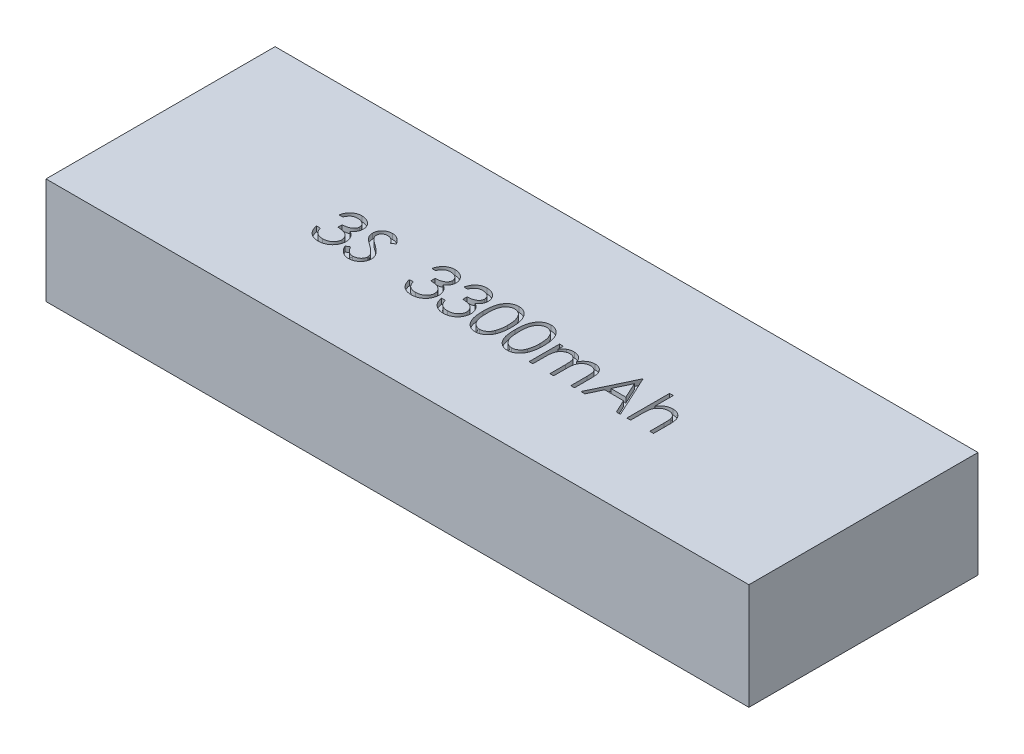
SolidWorks part; units mm, degrees
ref_plane "Front Plane" through (0, 0, 0) normal (0, 0, 1) x (1, 0, 0)
ref_plane "Top Plane" through (0, 0, 0) normal (0, 1, 0) x (1, 0, 0)
ref_plane "Right Plane" through (0, 0, 0) normal (1, 0, 0) x (0, 0, -1)
sketch "Sketch1" plane through (0, 0, 0) normal (0, 1, 0) x (1, 0, 0)
  line L1 (0, 0) -> (135, 0)
  line L2 (0, 0) -> (0, 44)
  line L3 (0, 44) -> (135, 44)
  line L4 (135, 0) -> (135, 44)
  dimension "D1" = 135
  dimension "D2" = 44
extrude "Boss-Extrude1" add sketch "Sketch1" along normal blind 20.4
sketch "Sketch2" plane through (0, 20.4, 0) normal (0, 1, 0) x (1, 0, 0)
  line L0 (0, 16) -> (135, 16) construction
  line L1 (0, 44) -> (0, 0) construction
  line L2 (135, 0) -> (135, 44) construction
  line L3 (0, 0) -> (135, 0) construction
  text T0 "3S  3300mAh" font "Century Gothic" height 8
  dimension "D1" = 16
extrude "Cut-Extrude1" cut sketch "Sketch2" against normal blind 1
